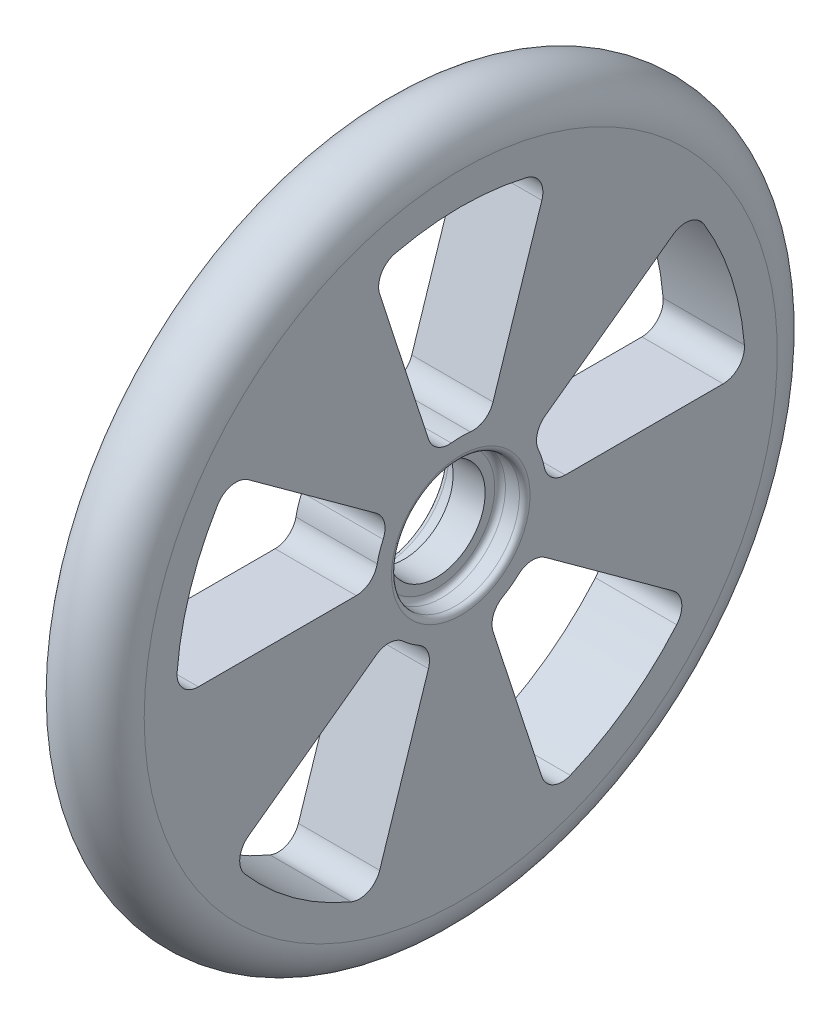
SolidWorks part; units mm, degrees
ref_plane "Front Plane" through (0, 0, 0) normal (0, 0, 1) x (1, 0, 0)
ref_plane "Top Plane" through (0, 0, 0) normal (0, 1, 0) x (1, 0, 0)
ref_plane "Right Plane" through (0, 0, 0) normal (1, 0, 0) x (0, 0, -1)
sketch "Sketch3" plane through (0, 0, 0) normal (0, 0, 1) x (1, 0, 0)
  line L0 (0, 0) -> (10.5995, 0) construction
  line L1 (0, 0) -> (0, 29.69) construction
  line L2 (-1.5, 4.6) -> (1.5, 4.6)
  line L3 (1.5, 4.6) -> (1.5, 5.5)
  line L4 (2, 6) -> (3.31, 6)
  line L5 (3.81, 6.5) -> (3.81, 29.69)
  line L6 (-3.81, 6.5) -> (-3.81, 29.69)
  line L7 (-2, 6) -> (-3.31, 6)
  line L8 (-1.5, 4.6) -> (-1.5, 5.5)
  arc A0 (1.5, 5.5) -> (2, 6) centre (2, 5.5) cw
  arc A1 (3.31, 6) -> (3.81, 6.5) centre (3.31, 6.5) ccw
  arc A4 (-3.31, 6) -> (-3.81, 6.5) centre (-3.31, 6.5) cw
  arc A5 (-1.5, 5.5) -> (-2, 6) centre (-2, 5.5) ccw
  arc A6 (3.81, 29.69) -> (-3.81, 29.69) centre (0, 29.69) ccw
  point P3 (-1.5, 4.6)
  point P4 (0, 33.5)
  point P12 (1.5, 6)
  point P15 (3.81, 6)
  point P18 (1.5, 4.6)
  point P29 (0, 4.6)
  point P30 (-3.81, 6)
  point P31 (-1.5, 6)
  dimension "D6" = 0.5
  dimension "D1" = 1.5
  dimension "D2" = 4.6
  dimension "D3" = 33.5
  dimension "D4" = 3.81
  dimension "D5" = 6
revolve "Revolve1" add sketch "Sketch3" angle 360 about L0
sketch "Sketch6" plane through (3.81, 0, 0) normal (1, 0, 0) x (0, 0, -1)
  line L0 (7.9267, 5.7591) -> (19.909, 14.4647)
  line L1 (24.6089, 0) -> (9.798, 0)
  line L2 (0, 0) -> (19.5288, 0) construction
  line L3 (0, 0) -> (0, 5.2799) construction
  line L4 (26.69, 0) -> (0, 0) construction
  line L5 (21.5927, 15.688) -> (0, 0) construction
  circle A0 centre (0, 0) radius 6.5 construction
  arc A2 (7.2818, 3.3128) -> (7.8384, 1.6) centre (0, 0) cw
  arc A3 (22.7925, 13.8873) -> (26.6023, 2.162) centre (0, 0) cw
  circle A4 centre (0, 0) radius 29.69 construction
  arc A5 (9.798, 0) -> (7.8384, 1.6) centre (9.798, 2) cw
  arc A6 (7.9267, 5.7591) -> (7.2818, 3.3128) centre (9.1023, 4.1411) ccw
  arc A7 (24.6089, 0) -> (26.6023, 2.162) centre (24.6089, 2) ccw
  arc A8 (19.909, 14.4647) -> (22.7925, 13.8873) centre (21.0846, 12.8467) cw
  dimension "D1" = 36
  dimension "D3" = 1.5
  dimension "D4" = 3
  dimension "D2" = 2
extrude "Cut-Extrude1" cut sketch "Sketch6" against normal up to next (7.62 mm away)
pattern_circular "CirPattern1" count 5 over 360 about axis through (0, 0, 0) along (1, 0, 0) of "Cut-Extrude1"
